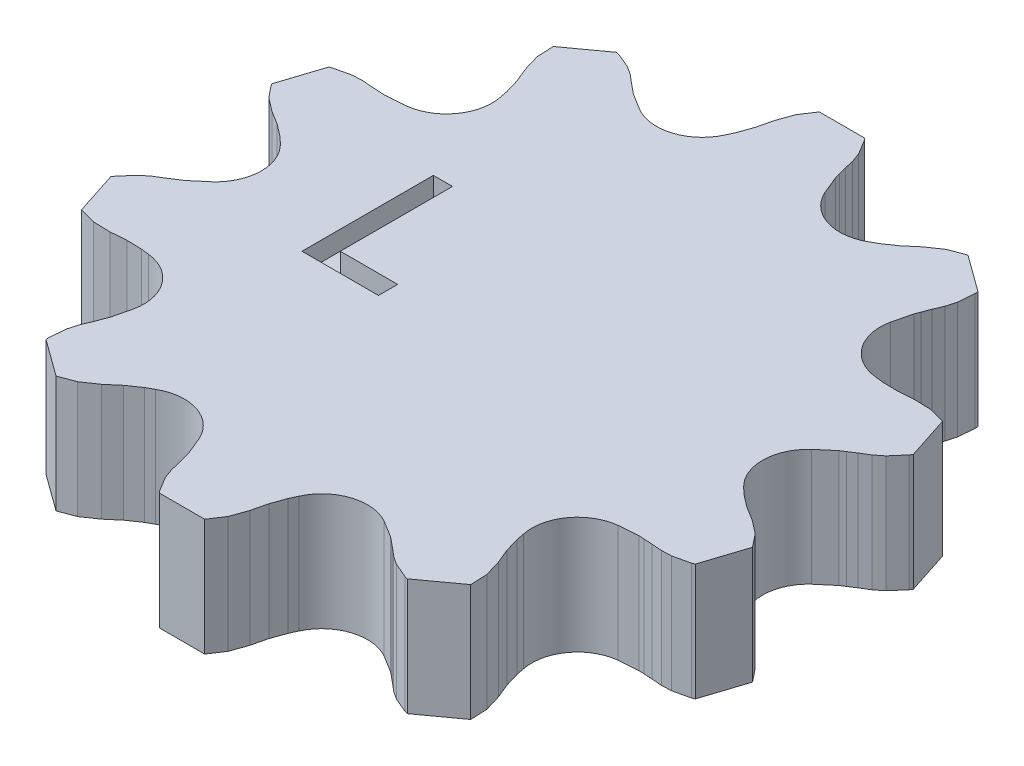
SolidWorks part; units mm, degrees
ref_plane "Front Plane" through (0, 0, 0) normal (0, 0, 1) x (1, 0, 0)
ref_plane "Top Plane" through (0, 0, 0) normal (0, 1, 0) x (1, 0, 0)
ref_plane "Right Plane" through (0, 0, 0) normal (1, 0, 0) x (0, 0, -1)
sketch "Sketch1" plane through (0, 0, 0) normal (0, 1, 0) x (1, 0, 0)
  line L0 (0, 0) -> (0, 13.7351) construction
  line L1 (-12.5202, 9.0964) -> (-4.7823, 14.7183) construction
  circle A0 centre (-4.7823, 14.7183) radius 2.3902 construction
  circle A1 centre (-12.5202, 9.0964) radius 2.3902 construction
  arc A2 (-2.6037, 13.7351) -> (-5.9668, 12.6424) centre (-4.7823, 14.7183) cw
  arc A3 (5.9668, 12.6424) -> (2.6037, 13.7351) centre (4.7823, 14.7183) cw
  arc A4 (12.2583, 6.7207) -> (10.1798, 9.5815) centre (12.5202, 9.0964) cw
  arc A5 (13.8675, -1.7681) -> (13.8675, 1.7681) centre (15.4758, 0) cw
  arc A6 (10.1798, -9.5815) -> (12.2583, -6.7207) centre (12.5202, -9.0964) cw
  arc A7 (2.6037, -13.7351) -> (5.9668, -12.6424) centre (4.7823, -14.7183) cw
  arc A8 (-5.9668, -12.6424) -> (-2.6037, -13.7351) centre (-4.7823, -14.7183) cw
  arc A9 (-12.2583, -6.7207) -> (-10.1798, -9.5815) centre (-12.5202, -9.0964) cw
  arc A10 (-13.8675, 1.7681) -> (-13.8675, -1.7681) centre (-15.4758, 0) cw
  arc A11 (-10.1798, 9.5815) -> (-12.2583, 6.7207) centre (-12.5202, 9.0964) cw
  point P1 (0, 0)
  point P4 (0, 0)
  point P5 (0, 0)
  point P40 (0, 0)
  line B0 (-2.6037, 13.7351) -> (2.6037, 13.7351) construction
  line B1 (-1.1874, 17.2351) -> (1.1848, 17.2351)
  line B2 (-2.6037, 13.7351) -> (-2.4267, 14.1152)
  line B3 (-2.4267, 14.1152) -> (-2.1621, 14.8638)
  line B4 (-2.1621, 14.8638) -> (-1.9701, 15.6613)
  line B5 (-1.9701, 15.6613) -> (-1.6716, 16.5006)
  line B6 (-1.6716, 16.5006) -> (-1.1874, 17.2351)
  line B7 (1.1848, 17.2351) -> (1.2836, 17.1136)
  line B8 (1.2836, 17.1136) -> (1.7287, 16.3759)
  line B9 (1.7287, 16.3759) -> (1.9084, 15.8861)
  line B10 (1.9084, 15.8861) -> (2.0293, 15.3825)
  line B11 (2.0293, 15.3825) -> (2.1437, 14.9484)
  line B12 (2.1437, 14.9484) -> (2.2127, 14.688)
  line B13 (2.2127, 14.688) -> (2.6037, 13.7351)
  line B14 (5.9668, 12.6424) -> (10.1798, 9.5815) construction
  line B15 (9.1699, 14.6414) -> (11.089, 13.2471)
  line B16 (5.9668, 12.6424) -> (6.3335, 12.8458)
  line B17 (6.3335, 12.8458) -> (6.9876, 13.2959)
  line B18 (6.9876, 13.2959) -> (7.6116, 13.8282)
  line B19 (7.6116, 13.8282) -> (8.3465, 14.3318)
  line B20 (8.3465, 14.3318) -> (9.1699, 14.6414)
  line B21 (11.089, 13.2471) -> (11.0976, 13.0907)
  line B22 (11.0976, 13.0907) -> (11.024, 12.2322)
  line B23 (11.024, 12.2322) -> (10.8816, 11.7304)
  line B24 (10.8816, 11.7304) -> (10.6834, 11.2519)
  line B25 (10.6834, 11.2519) -> (10.5207, 10.8335)
  line B26 (10.5207, 10.8335) -> (10.4235, 10.5822)
  line B27 (10.4235, 10.5822) -> (10.1798, 9.5815)
  line B28 (12.2583, 6.7207) -> (13.8675, 1.7681) construction
  line B29 (16.0246, 6.4552) -> (16.7577, 4.1991)
  line B30 (12.2583, 6.7207) -> (12.6745, 6.6698)
  line B31 (12.6745, 6.6698) -> (13.4682, 6.6494)
  line B32 (13.4682, 6.6494) -> (14.286, 6.7133)
  line B33 (14.286, 6.7133) -> (15.1765, 6.6887)
  line B34 (15.1765, 6.6887) -> (16.0246, 6.4552)
  line B35 (16.7577, 4.1991) -> (16.6727, 4.0676)
  line B36 (16.6727, 4.0676) -> (16.1086, 3.4163)
  line B37 (16.1086, 3.4163) -> (15.6983, 3.0941)
  line B38 (15.6983, 3.0941) -> (15.2568, 2.8234)
  line B39 (15.2568, 2.8234) -> (14.8792, 2.5805)
  line B40 (14.8792, 2.5805) -> (14.6529, 2.4344)
  line B41 (14.6529, 2.4344) -> (13.8675, 1.7681)
  line B42 (13.8675, -1.7681) -> (12.2583, -6.7207) construction
  line B43 (16.7585, -4.1967) -> (16.0254, -6.4527)
  line B44 (13.8675, -1.7681) -> (14.1743, -2.0539)
  line B45 (14.1743, -2.0539) -> (14.8044, -2.5369)
  line B46 (14.8044, -2.5369) -> (15.5035, -2.9659)
  line B47 (15.5035, -2.9659) -> (16.2096, -3.5092)
  line B48 (16.2096, -3.5092) -> (16.7585, -4.1967)
  line B49 (16.0254, -6.4527) -> (15.8793, -6.5092)
  line B50 (15.8793, -6.5092) -> (15.0402, -6.7045)
  line B51 (15.0402, -6.7045) -> (14.5189, -6.7241)
  line B52 (14.5189, -6.7241) -> (14.0026, -6.6835)
  line B53 (14.0026, -6.6835) -> (13.5543, -6.6581)
  line B54 (13.5543, -6.6581) -> (13.2854, -6.6432)
  line B55 (13.2854, -6.6432) -> (12.2583, -6.7207)
  line B56 (10.1798, -9.5815) -> (5.9668, -12.6424) construction
  line B57 (11.0911, -13.2456) -> (9.172, -14.6399)
  line B58 (10.1798, -9.5815) -> (10.26, -9.9931)
  line B59 (10.26, -9.9931) -> (10.4858, -10.7542)
  line B60 (10.4858, -10.7542) -> (10.7993, -11.5122)
  line B61 (10.7993, -11.5122) -> (11.0511, -12.3668)
  line B62 (11.0511, -12.3668) -> (11.0911, -13.2456)
  line B63 (9.172, -14.6399) -> (9.0207, -14.5997)
  line B64 (9.0207, -14.5997) -> (8.2269, -14.2645)
  line B65 (8.2269, -14.2645) -> (7.7937, -13.9739)
  line B66 (7.7937, -13.9739) -> (7.3999, -13.6376)
  line B67 (7.3999, -13.6376) -> (7.0522, -13.3535)
  line B68 (7.0522, -13.3535) -> (6.8433, -13.1834)
  line B69 (6.8433, -13.1834) -> (5.9668, -12.6424)
  line B70 (2.6037, -13.7351) -> (-2.6037, -13.7351) construction
  line B71 (1.1874, -17.2351) -> (-1.1848, -17.2351)
  line B72 (2.6037, -13.7351) -> (2.4267, -14.1152)
  line B73 (2.4267, -14.1152) -> (2.1621, -14.8638)
  line B74 (2.1621, -14.8638) -> (1.9701, -15.6613)
  line B75 (1.9701, -15.6613) -> (1.6716, -16.5006)
  line B76 (1.6716, -16.5006) -> (1.1874, -17.2351)
  line B77 (-1.1848, -17.2351) -> (-1.2836, -17.1136)
  line B78 (-1.2836, -17.1136) -> (-1.7287, -16.3759)
  line B79 (-1.7287, -16.3759) -> (-1.9084, -15.8861)
  line B80 (-1.9084, -15.8861) -> (-2.0293, -15.3825)
  line B81 (-2.0293, -15.3825) -> (-2.1437, -14.9484)
  line B82 (-2.1437, -14.9484) -> (-2.2127, -14.688)
  line B83 (-2.2127, -14.688) -> (-2.6037, -13.7351)
  line B84 (-5.9668, -12.6424) -> (-10.1798, -9.5815) construction
  line B85 (-9.1699, -14.6414) -> (-11.089, -13.2471)
  line B86 (-5.9668, -12.6424) -> (-6.3335, -12.8458)
  line B87 (-6.3335, -12.8458) -> (-6.9876, -13.2959)
  line B88 (-6.9876, -13.2959) -> (-7.6116, -13.8282)
  line B89 (-7.6116, -13.8282) -> (-8.3465, -14.3318)
  line B90 (-8.3465, -14.3318) -> (-9.1699, -14.6414)
  line B91 (-11.089, -13.2471) -> (-11.0976, -13.0907)
  line B92 (-11.0976, -13.0907) -> (-11.024, -12.2322)
  line B93 (-11.024, -12.2322) -> (-10.8816, -11.7304)
  line B94 (-10.8816, -11.7304) -> (-10.6834, -11.2519)
  line B95 (-10.6834, -11.2519) -> (-10.5207, -10.8335)
  line B96 (-10.5207, -10.8335) -> (-10.4235, -10.5822)
  line B97 (-10.4235, -10.5822) -> (-10.1798, -9.5815)
  line B98 (-12.2583, -6.7207) -> (-13.8675, -1.7681) construction
  line B99 (-16.0246, -6.4552) -> (-16.7577, -4.1991)
  line B100 (-12.2583, -6.7207) -> (-12.6745, -6.6698)
  line B101 (-12.6745, -6.6698) -> (-13.4682, -6.6494)
  line B102 (-13.4682, -6.6494) -> (-14.286, -6.7133)
  line B103 (-14.286, -6.7133) -> (-15.1765, -6.6887)
  line B104 (-15.1765, -6.6887) -> (-16.0246, -6.4552)
  line B105 (-16.7577, -4.1991) -> (-16.6727, -4.0676)
  line B106 (-16.6727, -4.0676) -> (-16.1086, -3.4163)
  line B107 (-16.1086, -3.4163) -> (-15.6983, -3.0941)
  line B108 (-15.6983, -3.0941) -> (-15.2568, -2.8234)
  line B109 (-15.2568, -2.8234) -> (-14.8792, -2.5805)
  line B110 (-14.8792, -2.5805) -> (-14.6529, -2.4344)
  line B111 (-14.6529, -2.4344) -> (-13.8675, -1.7681)
  line B112 (-13.8675, 1.7681) -> (-12.2583, 6.7207) construction
  line B113 (-16.7585, 4.1967) -> (-16.0254, 6.4527)
  line B114 (-13.8675, 1.7681) -> (-14.1743, 2.0539)
  line B115 (-14.1743, 2.0539) -> (-14.8044, 2.5369)
  line B116 (-14.8044, 2.5369) -> (-15.5035, 2.9659)
  line B117 (-15.5035, 2.9659) -> (-16.2096, 3.5092)
  line B118 (-16.2096, 3.5092) -> (-16.7585, 4.1967)
  line B119 (-16.0254, 6.4527) -> (-15.8793, 6.5092)
  line B120 (-15.8793, 6.5092) -> (-15.0402, 6.7045)
  line B121 (-15.0402, 6.7045) -> (-14.5189, 6.7241)
  line B122 (-14.5189, 6.7241) -> (-14.0026, 6.6835)
  line B123 (-14.0026, 6.6835) -> (-13.5543, 6.6581)
  line B124 (-13.5543, 6.6581) -> (-13.2854, 6.6432)
  line B125 (-13.2854, 6.6432) -> (-12.2583, 6.7207)
  line B126 (-10.1798, 9.5815) -> (-5.9668, 12.6424) construction
  line B127 (-11.0911, 13.2456) -> (-9.172, 14.6399)
  line B128 (-10.1798, 9.5815) -> (-10.26, 9.9931)
  line B129 (-10.26, 9.9931) -> (-10.4858, 10.7542)
  line B130 (-10.4858, 10.7542) -> (-10.7993, 11.5122)
  line B131 (-10.7993, 11.5122) -> (-11.0511, 12.3668)
  line B132 (-11.0511, 12.3668) -> (-11.0911, 13.2456)
  line B133 (-9.172, 14.6399) -> (-9.0207, 14.5997)
  line B134 (-9.0207, 14.5997) -> (-8.2269, 14.2645)
  line B135 (-8.2269, 14.2645) -> (-7.7937, 13.9739)
  line B136 (-7.7937, 13.9739) -> (-7.3999, 13.6376)
  line B137 (-7.3999, 13.6376) -> (-7.0522, 13.3535)
  line B138 (-7.0522, 13.3535) -> (-6.8433, 13.1834)
  line B139 (-6.8433, 13.1834) -> (-5.9668, 12.6424)
  dimension "D1" = 4.7803
  dimension "D4" = 10
  dimension "D3" = 9.5646
  dimension "D2" = 10
sketch_block_instance "Block1-1"
sketch_block "Block1" parameters "D1"=5.2075
sketch_block_instance "Block1-2"
sketch_block_instance "Block1-3"
sketch_block_instance "Block1-4"
sketch_block_instance "Block1-5"
sketch_block_instance "Block1-6"
sketch_block_instance "Block1-7"
sketch_block_instance "Block1-8"
sketch_block_instance "Block1-9"
sketch_block_instance "Block1-10"
sketch "Sketch2" plane through (0, 0, 0) normal (0, 0, 1) x (1, 0, 0)
  line L0 (0, 0) -> (0, 13.7351)
  line L1 (-12.5202, 9.0964) -> (-4.7823, 14.7183) construction
  circle A0 centre (-4.7823, 14.7183) radius 2.3902 construction
  circle A1 centre (-12.5202, 9.0964) radius 2.3902 construction
  point P1 (-14.1673, 12.6648)
  point P4 (8.4356, 4.9212)
  point P5 (0, 0)
  point P6 (0, 0)
  point P7 (0, 0)
  point P8 (0, 0)
  point P9 (0, 13.3739)
  point P12 (0, 0)
  point P15 (-14.0872, 10.2401)
  point P16 (0, 0)
  point P18 (0, 0)
  point P19 (0, 13.168)
  point P20 (-12.6118, 9.2107)
  point P21 (0, 0)
  line B0 (-2.6037, 13.7351) -> (2.6037, 13.7351) construction
  line B1 (-1.1874, 17.2351) -> (1.1848, 17.2351)
  line B2 (-2.6037, 13.7351) -> (-2.4267, 14.1152)
  line B3 (-2.4267, 14.1152) -> (-2.1621, 14.8638)
  line B4 (-2.1621, 14.8638) -> (-1.9701, 15.6613)
  line B5 (-1.9701, 15.6613) -> (-1.6716, 16.5006)
  line B6 (-1.6716, 16.5006) -> (-1.1874, 17.2351)
  line B7 (1.1848, 17.2351) -> (1.2836, 17.1136)
  line B8 (1.2836, 17.1136) -> (1.7287, 16.3759)
  line B9 (1.7287, 16.3759) -> (1.9084, 15.8861)
  line B10 (1.9084, 15.8861) -> (2.0293, 15.3825)
  line B11 (2.0293, 15.3825) -> (2.1437, 14.9484)
  line B12 (2.1437, 14.9484) -> (2.2127, 14.688)
  line B13 (2.2127, 14.688) -> (2.6037, 13.7351)
  line B14 (5.9668, 12.6424) -> (10.1798, 9.5815) construction
  line B15 (9.1699, 14.6414) -> (11.089, 13.2471)
  line B16 (5.9668, 12.6424) -> (6.3335, 12.8458)
  line B17 (6.3335, 12.8458) -> (6.9876, 13.2959)
  line B18 (6.9876, 13.2959) -> (7.6116, 13.8282)
  line B19 (7.6116, 13.8282) -> (8.3465, 14.3318)
  line B20 (8.3465, 14.3318) -> (9.1699, 14.6414)
  line B21 (11.089, 13.2471) -> (11.0976, 13.0907)
  line B22 (11.0976, 13.0907) -> (11.024, 12.2322)
  line B23 (11.024, 12.2322) -> (10.8816, 11.7304)
  line B24 (10.8816, 11.7304) -> (10.6834, 11.2519)
  line B25 (10.6834, 11.2519) -> (10.5207, 10.8335)
  line B26 (10.5207, 10.8335) -> (10.4235, 10.5822)
  line B27 (10.4235, 10.5822) -> (10.1798, 9.5815)
  line B28 (12.2583, 6.7207) -> (13.8675, 1.7681) construction
  line B29 (16.0246, 6.4552) -> (16.7577, 4.1991)
  line B30 (12.2583, 6.7207) -> (12.6745, 6.6698)
  line B31 (12.6745, 6.6698) -> (13.4682, 6.6494)
  line B32 (13.4682, 6.6494) -> (14.286, 6.7133)
  line B33 (14.286, 6.7133) -> (15.1765, 6.6887)
  line B34 (15.1765, 6.6887) -> (16.0246, 6.4552)
  line B35 (16.7577, 4.1991) -> (16.6727, 4.0676)
  line B36 (16.6727, 4.0676) -> (16.1086, 3.4163)
  line B37 (16.1086, 3.4163) -> (15.6983, 3.0941)
  line B38 (15.6983, 3.0941) -> (15.2568, 2.8234)
  line B39 (15.2568, 2.8234) -> (14.8792, 2.5805)
  line B40 (14.8792, 2.5805) -> (14.6529, 2.4344)
  line B41 (14.6529, 2.4344) -> (13.8675, 1.7681)
  line B42 (13.8675, -1.7681) -> (12.2583, -6.7207) construction
  line B43 (16.7585, -4.1967) -> (16.0254, -6.4527)
  line B44 (13.8675, -1.7681) -> (14.1743, -2.0539)
  line B45 (14.1743, -2.0539) -> (14.8044, -2.5369)
  line B46 (14.8044, -2.5369) -> (15.5035, -2.9659)
  line B47 (15.5035, -2.9659) -> (16.2096, -3.5092)
  line B48 (16.2096, -3.5092) -> (16.7585, -4.1967)
  line B49 (16.0254, -6.4527) -> (15.8793, -6.5092)
  line B50 (15.8793, -6.5092) -> (15.0402, -6.7045)
  line B51 (15.0402, -6.7045) -> (14.5189, -6.7241)
  line B52 (14.5189, -6.7241) -> (14.0026, -6.6835)
  line B53 (14.0026, -6.6835) -> (13.5543, -6.6581)
  line B54 (13.5543, -6.6581) -> (13.2854, -6.6432)
  line B55 (13.2854, -6.6432) -> (12.2583, -6.7207)
  line B56 (10.1798, -9.5815) -> (5.9668, -12.6424) construction
  line B57 (11.0911, -13.2456) -> (9.172, -14.6399)
  line B58 (10.1798, -9.5815) -> (10.26, -9.9931)
  line B59 (10.26, -9.9931) -> (10.4858, -10.7542)
  line B60 (10.4858, -10.7542) -> (10.7993, -11.5122)
  line B61 (10.7993, -11.5122) -> (11.0511, -12.3668)
  line B62 (11.0511, -12.3668) -> (11.0911, -13.2456)
  line B63 (9.172, -14.6399) -> (9.0207, -14.5997)
  line B64 (9.0207, -14.5997) -> (8.2269, -14.2645)
  line B65 (8.2269, -14.2645) -> (7.7937, -13.9739)
  line B66 (7.7937, -13.9739) -> (7.3999, -13.6376)
  line B67 (7.3999, -13.6376) -> (7.0522, -13.3535)
  line B68 (7.0522, -13.3535) -> (6.8433, -13.1834)
  line B69 (6.8433, -13.1834) -> (5.9668, -12.6424)
  line B70 (2.6037, -13.7351) -> (-2.6037, -13.7351) construction
  line B71 (1.1874, -17.2351) -> (-1.1848, -17.2351)
  line B72 (2.6037, -13.7351) -> (2.4267, -14.1152)
  line B73 (2.4267, -14.1152) -> (2.1621, -14.8638)
  line B74 (2.1621, -14.8638) -> (1.9701, -15.6613)
  line B75 (1.9701, -15.6613) -> (1.6716, -16.5006)
  line B76 (1.6716, -16.5006) -> (1.1874, -17.2351)
  line B77 (-1.1848, -17.2351) -> (-1.2836, -17.1136)
  line B78 (-1.2836, -17.1136) -> (-1.7287, -16.3759)
  line B79 (-1.7287, -16.3759) -> (-1.9084, -15.8861)
  line B80 (-1.9084, -15.8861) -> (-2.0293, -15.3825)
  line B81 (-2.0293, -15.3825) -> (-2.1437, -14.9484)
  line B82 (-2.1437, -14.9484) -> (-2.2127, -14.688)
  line B83 (-2.2127, -14.688) -> (-2.6037, -13.7351)
  line B84 (-5.9668, -12.6424) -> (-10.1798, -9.5815) construction
  line B85 (-9.1699, -14.6414) -> (-11.089, -13.2471)
  line B86 (-5.9668, -12.6424) -> (-6.3335, -12.8458)
  line B87 (-6.3335, -12.8458) -> (-6.9876, -13.2959)
  line B88 (-6.9876, -13.2959) -> (-7.6116, -13.8282)
  line B89 (-7.6116, -13.8282) -> (-8.3465, -14.3318)
  line B90 (-8.3465, -14.3318) -> (-9.1699, -14.6414)
  line B91 (-11.089, -13.2471) -> (-11.0976, -13.0907)
  line B92 (-11.0976, -13.0907) -> (-11.024, -12.2322)
  line B93 (-11.024, -12.2322) -> (-10.8816, -11.7304)
  line B94 (-10.8816, -11.7304) -> (-10.6834, -11.2519)
  line B95 (-10.6834, -11.2519) -> (-10.5207, -10.8335)
  line B96 (-10.5207, -10.8335) -> (-10.4235, -10.5822)
  line B97 (-10.4235, -10.5822) -> (-10.1798, -9.5815)
  line B98 (-12.2583, -6.7207) -> (-13.8675, -1.7681) construction
  line B99 (-16.0246, -6.4552) -> (-16.7577, -4.1991)
  line B100 (-12.2583, -6.7207) -> (-12.6745, -6.6698)
  line B101 (-12.6745, -6.6698) -> (-13.4682, -6.6494)
  line B102 (-13.4682, -6.6494) -> (-14.286, -6.7133)
  line B103 (-14.286, -6.7133) -> (-15.1765, -6.6887)
  line B104 (-15.1765, -6.6887) -> (-16.0246, -6.4552)
  line B105 (-16.7577, -4.1991) -> (-16.6727, -4.0676)
  line B106 (-16.6727, -4.0676) -> (-16.1086, -3.4163)
  line B107 (-16.1086, -3.4163) -> (-15.6983, -3.0941)
  line B108 (-15.6983, -3.0941) -> (-15.2568, -2.8234)
  line B109 (-15.2568, -2.8234) -> (-14.8792, -2.5805)
  line B110 (-14.8792, -2.5805) -> (-14.6529, -2.4344)
  line B111 (-14.6529, -2.4344) -> (-13.8675, -1.7681)
  line B112 (-13.8675, 1.7681) -> (-12.2583, 6.7207) construction
  line B113 (-16.7585, 4.1967) -> (-16.0254, 6.4527)
  line B114 (-13.8675, 1.7681) -> (-14.1743, 2.0539)
  line B115 (-14.1743, 2.0539) -> (-14.8044, 2.5369)
  line B116 (-14.8044, 2.5369) -> (-15.5035, 2.9659)
  line B117 (-15.5035, 2.9659) -> (-16.2096, 3.5092)
  line B118 (-16.2096, 3.5092) -> (-16.7585, 4.1967)
  line B119 (-16.0254, 6.4527) -> (-15.8793, 6.5092)
  line B120 (-15.8793, 6.5092) -> (-15.0402, 6.7045)
  line B121 (-15.0402, 6.7045) -> (-14.5189, 6.7241)
  line B122 (-14.5189, 6.7241) -> (-14.0026, 6.6835)
  line B123 (-14.0026, 6.6835) -> (-13.5543, 6.6581)
  line B124 (-13.5543, 6.6581) -> (-13.2854, 6.6432)
  line B125 (-13.2854, 6.6432) -> (-12.2583, 6.7207)
  line B126 (-10.1798, 9.5815) -> (-5.9668, 12.6424) construction
  line B127 (-11.0911, 13.2456) -> (-9.172, 14.6399)
  line B128 (-10.1798, 9.5815) -> (-10.26, 9.9931)
  line B129 (-10.26, 9.9931) -> (-10.4858, 10.7542)
  line B130 (-10.4858, 10.7542) -> (-10.7993, 11.5122)
  line B131 (-10.7993, 11.5122) -> (-11.0511, 12.3668)
  line B132 (-11.0511, 12.3668) -> (-11.0911, 13.2456)
  line B133 (-9.172, 14.6399) -> (-9.0207, 14.5997)
  line B134 (-9.0207, 14.5997) -> (-8.2269, 14.2645)
  line B135 (-8.2269, 14.2645) -> (-7.7937, 13.9739)
  line B136 (-7.7937, 13.9739) -> (-7.3999, 13.6376)
  line B137 (-7.3999, 13.6376) -> (-7.0522, 13.3535)
  line B138 (-7.0522, 13.3535) -> (-6.8433, 13.1834)
  line B139 (-6.8433, 13.1834) -> (-5.9668, 12.6424)
  dimension "D1" = 4.7803
  dimension "D3" = 9.5646
  dimension "D2" = 10
sketch_block_instance "Block1-11"
sketch_block_instance "Block1-12"
sketch_block_instance "Block1-13"
sketch_block_instance "Block1-14"
sketch_block_instance "Block1-15"
sketch_block_instance "Block1-16"
sketch_block_instance "Block1-17"
sketch_block_instance "Block1-18"
sketch_block_instance "Block1-19"
sketch_block_instance "Block1-20"
extrude "Boss-Extrude1" add sketch "Sketch1" along normal blind 6.1 contours B139 B138 B137 B136 B135 B134 B133 B127 B132 B131 B130 B129 B128 A11 B125 B124 B123 B122 B121 B120 B119 B113 B118 B117 B116 B115 B114 A10 B111 B110 B109 B108 B107 B106 B105 B99 B104 B103 B102 B101 B100 A9 B97 B96 B95 B94 B93 B92 B91 B85 B90
sketch "Sketch3" plane through (0, 6.1, 0) normal (0, 1, 0) x (1, 0, 0)
  line L0 (-8.3931, 4.2854) -> (-8.3931, -2.5757)
  line L1 (-8.3931, -2.5757) -> (-4.3964, -2.5757)
  line L2 (-4.3964, -2.5757) -> (-4.3964, -1.5757)
  line L3 (-4.3964, -1.5757) -> (-7.3931, -1.5757)
  line L4 (-7.3931, -1.5757) -> (-7.3931, 4.2854)
  line L5 (-7.3931, 4.2854) -> (-8.3931, 4.2854)
  dimension "D1" = 1
  dimension "D2" = 1
extrude "Cut-Extrude1" cut sketch "Sketch3" against normal blind 1
